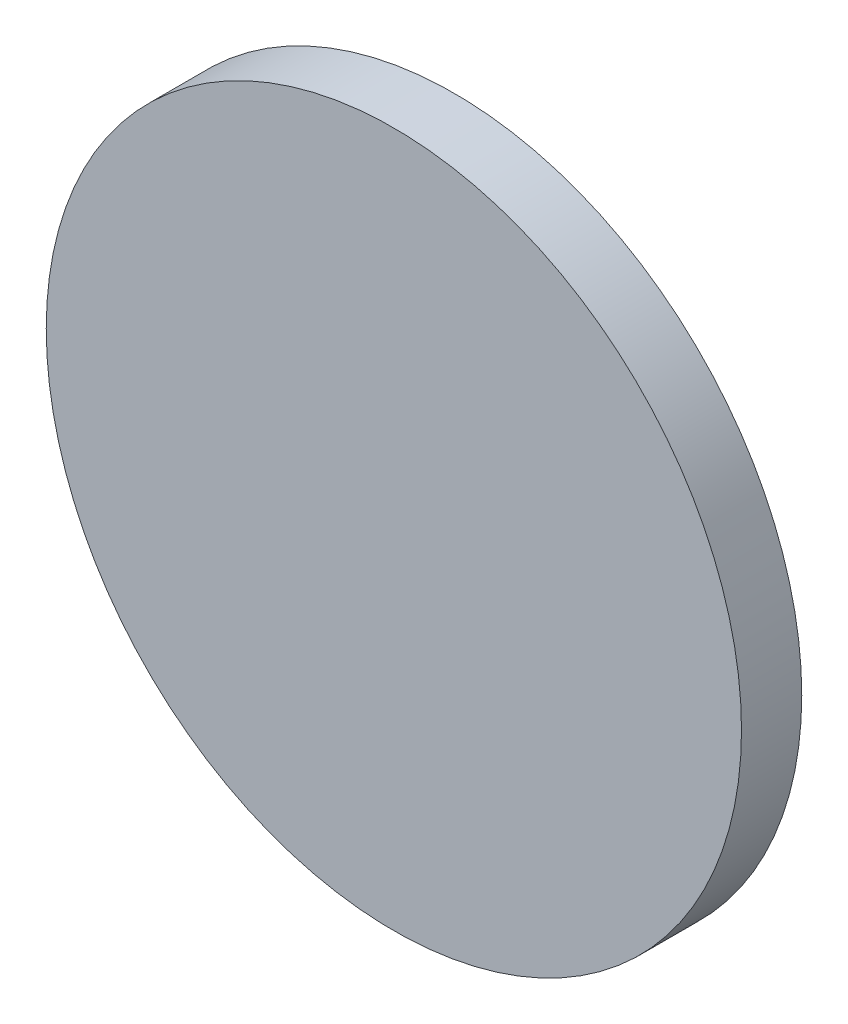
SolidWorks part; units mm, degrees
material "Bismuth"
ref_plane "Front" through (0, 0, 0) normal (0, 0, 1) x (1, 0, 0)
ref_plane "Top" through (0, 0, 0) normal (0, 1, 0) x (1, 0, 0)
ref_plane "Right" through (0, 0, 0) normal (1, 0, 0) x (0, 0, -1)
sketch "Sketch1" plane through (0, 0, 0) normal (0, 0, 1) x (1, 0, 0)
  circle A0 centre (0, 0) radius 75
extrude "Boss-Extrude1" add sketch "Sketch1" along normal blind 13
